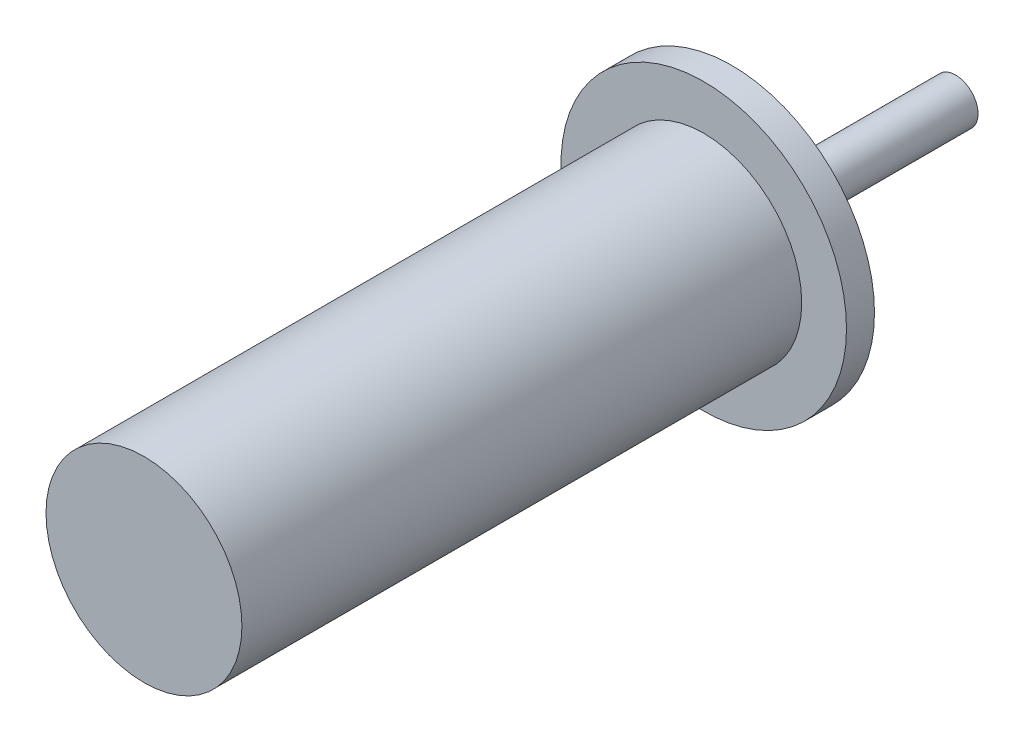
SolidWorks part; units mm, degrees
ref_plane "Front" through (0, 0, 0) normal (0, 0, 1) x (1, 0, 0)
ref_plane "Top" through (0, 0, 0) normal (0, 1, 0) x (1, 0, 0)
ref_plane "Right" through (0, 0, 0) normal (1, 0, 0) x (0, 0, -1)
sketch "Sketch1" plane through (0, 0, 0) normal (0, 0, 1) x (1, 0, 0)
  circle A2 centre (0, 0) radius 25.5
  dimension "D1" = 51
extrude "Boss-Extrude3" add sketch "Sketch1" along normal blind 5
sketch "Sketch3" plane through (0, 0, 5) normal (0, 0, 1) x (1, 0, 0)
  circle A0 centre (0, 0) radius 17.5
  dimension "D1" = 35
extrude "Boss-Extrude4" add sketch "Sketch3" along normal blind 100
sketch "Sketch4" plane through (0, 0, 0) normal (0, 0, -1) x (-1, 0, 0)
  circle A0 centre (0, 0) radius 4
  dimension "D1" = 8
extrude "Boss-Extrude5" add sketch "Sketch4" along normal blind 40
